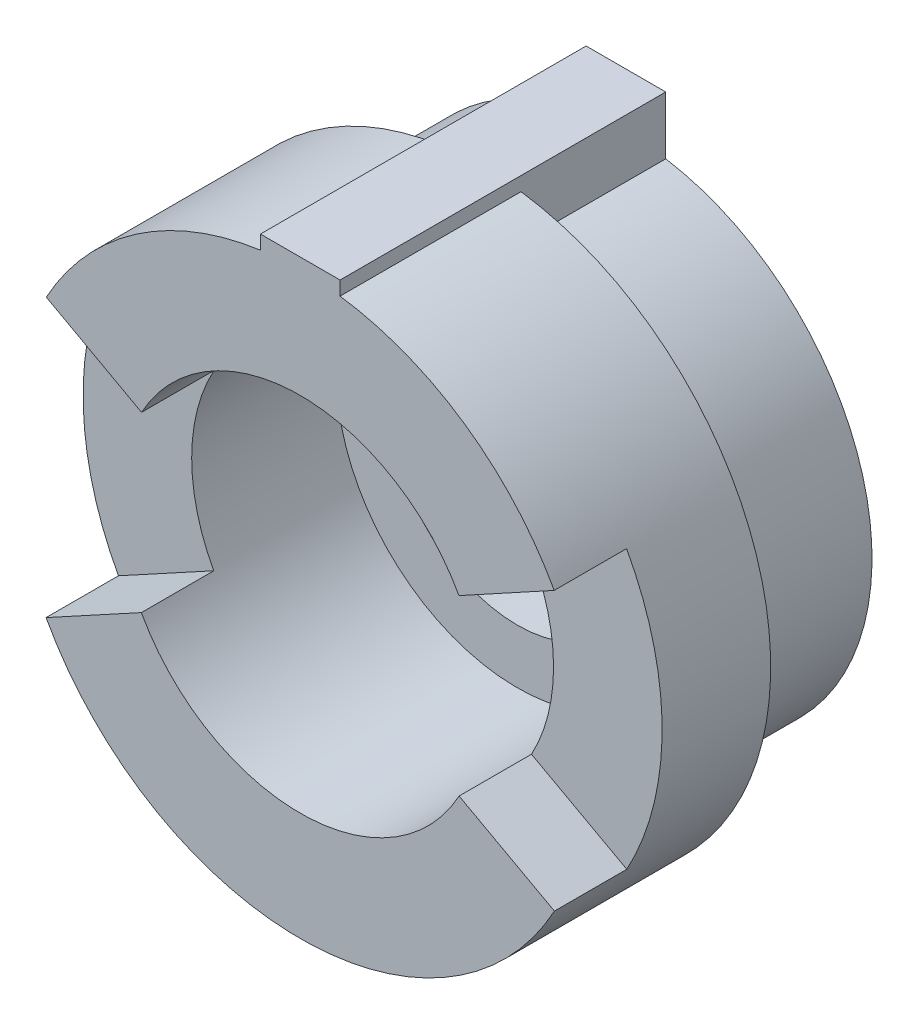
SolidWorks part; units mm, degrees
ref_plane "Front Plane" through (0, 0, 0) normal (0, 0, 1) x (1, 0, 0)
ref_plane "Top Plane" through (0, 0, 0) normal (0, 1, 0) x (1, 0, 0)
ref_plane "Right Plane" through (0, 0, 0) normal (1, 0, 0) x (0, 0, -1)
sketch "Sketch1" plane through (0, 0, 0) normal (0, 0, 1) x (1, 0, 0)
  circle A0 centre (0, 0) radius 8
  circle A1 centre (0, 0) radius 3.5
  dimension "D1" = 7
  dimension "D2" = 16
extrude "Boss-Extrude1" add sketch "Sketch1" along normal blind 3
sketch "Sketch2" plane through (0, 0, 3) normal (0, 0, 1) x (1, 0, 0)
  circle A0 centre (0, 0) radius 8
  circle A1 centre (0, 0) radius 5
  dimension "D1" = 16
  dimension "D2" = 10
extrude "Boss-Extrude2" add sketch "Sketch2" along normal blind 6
sketch "Sketch4" plane through (0, 0, 0) normal (0, 1, 0) x (1, 0, 0)
  line L0 (-8.56, -9) -> (-8.56, -7)
  line L1 (-16.56, -9) -> (-8.56, -9)
  line L2 (8.56, -9) -> (8.56, -7)
  line L3 (8.56, -9) -> (16.56, -9)
  line L4 (-16.56, -9) -> (-16.56, -7)
  line L5 (-16.56, -7) -> (-8.56, -7)
  line L6 (16.56, -9) -> (16.56, -7)
  line L7 (16.56, -7) -> (8.56, -7)
  dimension "D1" = 7
  dimension "D2" = 8.56
  dimension "D3" = 2
  dimension "D4" = 8.56
  dimension "D5" = 8
  dimension "D6" = 8
  dimension "D7" = 2
  dimension "D8" = 7
wrap "Wrap3" sketch "Sketch4" wrap type deboss source sketch "Sketch4" thickness 4 face at (8, 0, 0) parameters "D1"=4
sketch "Sketch5" plane through (0, 0, 0) normal (0, 0, -1) x (-1, 0, 0)
  line L0 (-1.1, 6.7104) -> (-1.1, 7.924)
  line L2 (1.1, 7.924) -> (1.1, 6.7104)
  arc A0 (-1.1, 7.924) -> (1.1, 7.924) centre (0, 0) ccw
  arc A1 (-1.1, 6.7104) -> (1.1, 6.7104) centre (0, 0) ccw
  circle A2 centre (0, 0) radius 8 construction
  dimension "D1" = 8
  dimension "D3" = 6.8
  dimension "D2" = 1.1
extrude "Cut-Extrude1" cut sketch "Sketch5" against normal blind 4
sketch "Sketch6" plane through (0, 0, 0) normal (0, 0, -1) x (-1, 0, 0)
  line L0 (-1.1, 7.7312) -> (-1.1, 8.3104)
  line L1 (-1.1, 8.3104) -> (1.1, 8.3104)
  line L2 (1.1, 8.3104) -> (1.1, 7.7312)
  line L3 (-1.1, 6.7104) -> (-1.1, 7.924) construction
  arc A0 (1.1, 7.7312) -> (-1.1, 7.7312) centre (0, -0.1929) ccw
  dimension "D1" = 8
  dimension "D2" = 1.1
  dimension "D3" = 1.0207
  dimension "D4" = 1.6
extrude "Boss-Extrude3" add sketch "Sketch6" against normal blind 9
equation "\"D3@Sketch5\"= 7 - \"tol1@parametersSketch@prostheticParameters.SLDPRT\" / 2"
equation "\"D2@Sketch5\"= 1.5 - \"tol2@parametersSketch@prostheticParameters.SLDPRT\""
equation "\"D2@Sketch6\"= 1.5 - \"tol2@parametersSketch@prostheticParameters.SLDPRT\""
equation "\"D4@Sketch6\"= 2 - \"tol2@parametersSketch@prostheticParameters.SLDPRT\""
